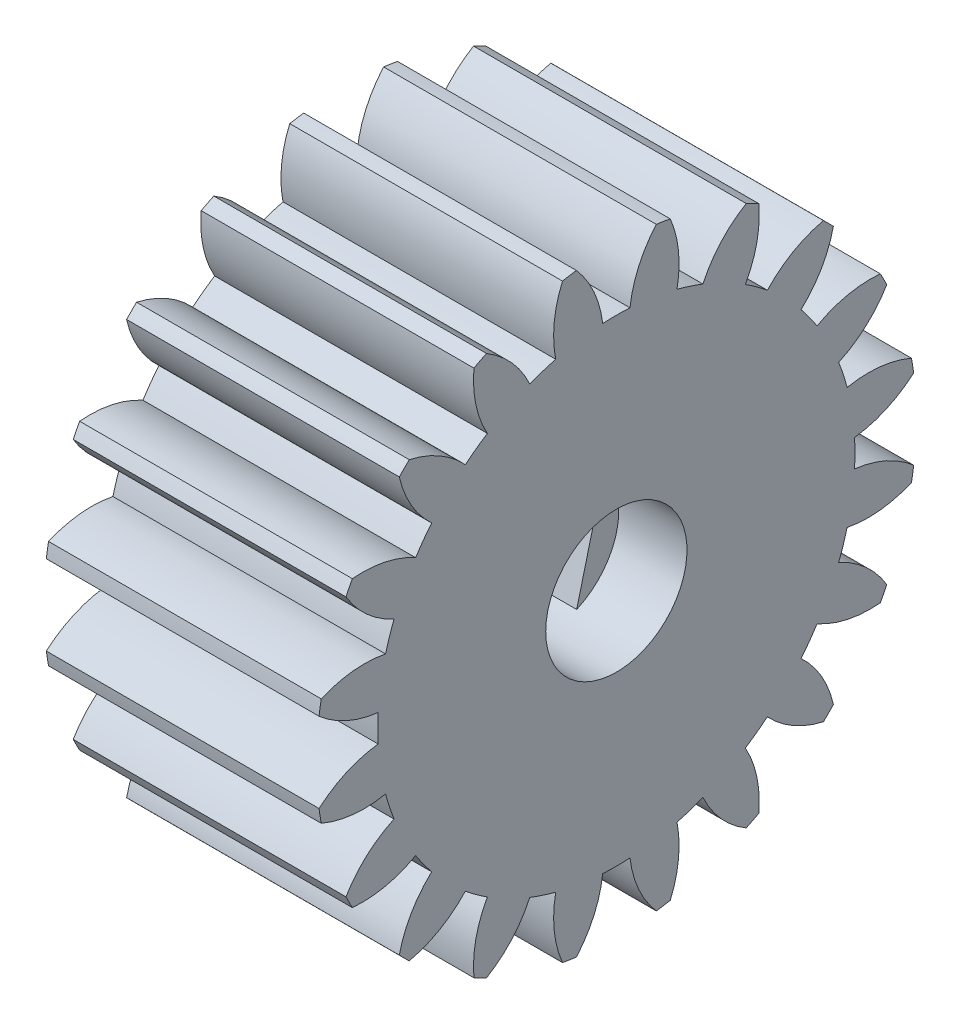
SolidWorks part; units mm, degrees
material "PLA"
ref_plane "Front Plane" through (0, 0, 0) normal (0, 0, 1) x (1, 0, 0)
ref_plane "Top Plane" through (0, 0, 0) normal (0, 1, 0) x (1, 0, 0)
ref_plane "Right Plane" through (0, 0, 0) normal (1, 0, 0) x (0, 0, -1)
ref_plane "Plane1" through (0, 0, 0) normal (0, 0, -1) x (-1, 0, 0)
sketch "Sketch1" plane through (0, 0, 0) normal (0, 0, -1) x (-1, 0, 0)
  line L0 (-10, 11) -> (-10, 0)
  line L1 (-10, 0) -> (0, 0)
  line L2 (0, 0) -> (0, 11)
  line L3 (0, 11) -> (-10, 11)
  line L4 (-10, 0) -> (0, 0) construction
revolve "Revolve1" add sketch "Sketch1" angle 360 about L4
sketch "Sketch2" plane through (0, 0, 0) normal (-1, 0, 0) x (0, 0, 1)
  arc A0 (10.8211, -1.9757) -> (8.4617, -2.2237) centre (9.242, 1.6994) cw
  arc A1 (8.4617, -2.2237) -> (8.1527, -3.1746) centre (0, 0) cw
  arc A2 (8.1527, -3.1746) -> (9.9157, -4.7622) centre (6.478, -6.8072) cw
  arc A3 (9.9157, -4.7622) -> (10.8211, -1.9757) centre (0, 0) ccw
extrude "Cut-Extrude1" cut sketch "Sketch2" against normal through all
sketch "Sketch3" plane through (0, 0, 0) normal (-1, 0, 0) x (0, 0, 1)
  arc A0 (9.681, -5.2229) -> (7.3604, -4.7297) centre (9.3148, -1.2397) cw
  arc A1 (7.3604, -4.7297) -> (6.7727, -5.5386) centre (0, 0) cw
  arc A2 (6.7727, -5.5386) -> (7.9588, -7.5932) centre (4.0574, -8.4758) cw
  arc A3 (7.9588, -7.5932) -> (9.681, -5.2229) centre (0, 0) ccw
extrude "Cut-Extrude2" cut sketch "Sketch3" against normal through all
sketch "Sketch4" plane through (0, 0, 0) normal (-1, 0, 0) x (0, 0, 1)
  arc A0 (5.2229, -9.681) -> (7.5932, -7.9588) centre (0, 0) ccw
  arc A1 (7.5932, -7.9588) -> (5.5386, -6.7727) centre (8.4758, -4.0574) cw
  arc A2 (5.5386, -6.7727) -> (4.7297, -7.3604) centre (0, 0) cw
  arc A3 (4.7297, -7.3604) -> (5.2229, -9.681) centre (1.2397, -9.3148) cw
extrude "Cut-Extrude3" cut sketch "Sketch4" against normal through all
sketch "Sketch5" plane through (0, 0, 0) normal (-1, 0, 0) x (0, 0, 1)
  arc A0 (1.9757, -10.8211) -> (4.7622, -9.9157) centre (0, 0) ccw
  arc A1 (4.7622, -9.9157) -> (3.1746, -8.1527) centre (6.8072, -6.478) cw
  arc A2 (3.1746, -8.1527) -> (2.2237, -8.4617) centre (0, 0) cw
  arc A3 (2.2237, -8.4617) -> (1.9757, -10.8211) centre (-1.6994, -9.242) cw
extrude "Cut-Extrude4" cut sketch "Sketch5" against normal through all
sketch "Sketch6" plane through (0, 0, 0) normal (-1, 0, 0) x (0, 0, 1)
  arc A0 (1.465, -10.902) -> (0.4999, -8.7347) centre (4.4722, -8.2645) cw
  arc A1 (0.4999, -8.7347) -> (-0.4999, -8.7347) centre (0, 0) cw
  arc A2 (-0.4999, -8.7347) -> (-1.465, -10.902) centre (-4.4722, -8.2645) cw
  arc A3 (-1.465, -10.902) -> (1.465, -10.902) centre (0, 0) ccw
extrude "Cut-Extrude5" cut sketch "Sketch6" against normal through all
sketch "Sketch7" plane through (0, 0, 0) normal (-1, 0, 0) x (0, 0, 1)
  arc A0 (-1.9757, -10.8211) -> (-2.2237, -8.4617) centre (1.6994, -9.242) cw
  arc A1 (-2.2237, -8.4617) -> (-3.1746, -8.1527) centre (0, 0) cw
  arc A2 (-3.1746, -8.1527) -> (-4.7622, -9.9157) centre (-6.8072, -6.478) cw
  arc A3 (-4.7622, -9.9157) -> (-1.9757, -10.8211) centre (0, 0) ccw
extrude "Cut-Extrude6" cut sketch "Sketch7" against normal through all
sketch "Sketch8" plane through (0, 0, 0) normal (-1, 0, 0) x (0, 0, 1)
  arc A0 (-5.2229, -9.681) -> (-4.7297, -7.3604) centre (-1.2397, -9.3148) cw
  arc A1 (-4.7297, -7.3604) -> (-5.5386, -6.7727) centre (0, 0) cw
  arc A2 (-5.5386, -6.7727) -> (-7.5932, -7.9588) centre (-8.4758, -4.0574) cw
  arc A3 (-7.5932, -7.9588) -> (-5.2229, -9.681) centre (0, 0) ccw
extrude "Cut-Extrude7" cut sketch "Sketch8" against normal through all
sketch "Sketch9" plane through (0, 0, 0) normal (-1, 0, 0) x (0, 0, 1)
  arc A0 (-7.9588, -7.5932) -> (-6.7727, -5.5386) centre (-4.0574, -8.4758) cw
  arc A1 (-6.7727, -5.5386) -> (-7.3604, -4.7297) centre (0, 0) cw
  arc A2 (-7.3604, -4.7297) -> (-9.681, -5.2229) centre (-9.3148, -1.2397) cw
  arc A3 (-9.681, -5.2229) -> (-7.9588, -7.5932) centre (0, 0) ccw
extrude "Cut-Extrude8" cut sketch "Sketch9" against normal through all
sketch "Sketch10" plane through (0, 0, 0) normal (-1, 0, 0) x (0, 0, 1)
  arc A0 (-9.9157, -4.7622) -> (-8.1527, -3.1746) centre (-6.478, -6.8072) cw
  arc A1 (-8.1527, -3.1746) -> (-8.4617, -2.2237) centre (0, 0) cw
  arc A2 (-8.4617, -2.2237) -> (-10.8211, -1.9757) centre (-9.242, 1.6994) cw
  arc A3 (-10.8211, -1.9757) -> (-9.9157, -4.7622) centre (0, 0) ccw
extrude "Cut-Extrude9" cut sketch "Sketch10" against normal through all
sketch "Sketch11" plane through (0, 0, 0) normal (-1, 0, 0) x (0, 0, 1)
  arc A0 (-10.902, -1.465) -> (-8.7347, -0.4999) centre (-8.2645, -4.4722) cw
  arc A1 (-8.7347, -0.4999) -> (-8.7347, 0.4999) centre (0, 0) cw
  arc A2 (-8.7347, 0.4999) -> (-10.902, 1.465) centre (-8.2645, 4.4722) cw
  arc A3 (-10.902, 1.465) -> (-10.902, -1.465) centre (0, 0) ccw
extrude "Cut-Extrude10" cut sketch "Sketch11" against normal through all
sketch "Sketch12" plane through (0, 0, 0) normal (-1, 0, 0) x (0, 0, 1)
  arc A0 (-10.8211, 1.9757) -> (-8.4617, 2.2237) centre (-9.242, -1.6994) cw
  arc A1 (-8.4617, 2.2237) -> (-8.1527, 3.1746) centre (0, 0) cw
  arc A2 (-8.1527, 3.1746) -> (-9.9157, 4.7622) centre (-6.478, 6.8072) cw
  arc A3 (-9.9157, 4.7622) -> (-10.8211, 1.9757) centre (0, 0) ccw
extrude "Cut-Extrude11" cut sketch "Sketch12" against normal through all
sketch "Sketch13" plane through (0, 0, 0) normal (-1, 0, 0) x (0, 0, 1)
  arc A0 (-9.681, 5.2229) -> (-7.3604, 4.7297) centre (-9.3148, 1.2397) cw
  arc A1 (-7.3604, 4.7297) -> (-6.7727, 5.5386) centre (0, 0) cw
  arc A2 (-6.7727, 5.5386) -> (-7.9588, 7.5932) centre (-4.0574, 8.4758) cw
  arc A3 (-7.9588, 7.5932) -> (-9.681, 5.2229) centre (0, 0) ccw
extrude "Cut-Extrude12" cut sketch "Sketch13" against normal through all
sketch "Sketch14" plane through (0, 0, 0) normal (-1, 0, 0) x (0, 0, 1)
  arc A0 (-7.5932, 7.9588) -> (-5.5386, 6.7727) centre (-8.4758, 4.0574) cw
  arc A1 (-5.5386, 6.7727) -> (-4.7297, 7.3604) centre (0, 0) cw
  arc A2 (-4.7297, 7.3604) -> (-5.2229, 9.681) centre (-1.2397, 9.3148) cw
  arc A3 (-5.2229, 9.681) -> (-7.5932, 7.9588) centre (0, 0) ccw
extrude "Cut-Extrude13" cut sketch "Sketch14" against normal through all
sketch "Sketch15" plane through (0, 0, 0) normal (-1, 0, 0) x (0, 0, 1)
  arc A0 (-4.7622, 9.9157) -> (-3.1746, 8.1527) centre (-6.8072, 6.478) cw
  arc A1 (-3.1746, 8.1527) -> (-2.2237, 8.4617) centre (0, 0) cw
  arc A2 (-2.2237, 8.4617) -> (-1.9757, 10.8211) centre (1.6994, 9.242) cw
  arc A3 (-1.9757, 10.8211) -> (-4.7622, 9.9157) centre (0, 0) ccw
extrude "Cut-Extrude14" cut sketch "Sketch15" against normal through all
sketch "Sketch16" plane through (0, 0, 0) normal (-1, 0, 0) x (0, 0, 1)
  arc A0 (-1.465, 10.902) -> (-0.4999, 8.7347) centre (-4.4722, 8.2645) cw
  arc A1 (-0.4999, 8.7347) -> (0.4999, 8.7347) centre (0, 0) cw
  arc A2 (0.4999, 8.7347) -> (1.465, 10.902) centre (4.4722, 8.2645) cw
  arc A3 (1.465, 10.902) -> (-1.465, 10.902) centre (0, 0) ccw
extrude "Cut-Extrude15" cut sketch "Sketch16" against normal through all
sketch "Sketch17" plane through (0, 0, 0) normal (-1, 0, 0) x (0, 0, 1)
  arc A0 (1.9757, 10.8211) -> (2.2237, 8.4617) centre (-1.6994, 9.242) cw
  arc A1 (2.2237, 8.4617) -> (3.1746, 8.1527) centre (0, 0) cw
  arc A2 (3.1746, 8.1527) -> (4.7622, 9.9157) centre (6.8072, 6.478) cw
  arc A3 (4.7622, 9.9157) -> (1.9757, 10.8211) centre (0, 0) ccw
extrude "Cut-Extrude16" cut sketch "Sketch17" against normal through all
sketch "Sketch18" plane through (0, 0, 0) normal (-1, 0, 0) x (0, 0, 1)
  arc A0 (5.2229, 9.681) -> (4.7297, 7.3604) centre (1.2397, 9.3148) cw
  arc A1 (4.7297, 7.3604) -> (5.5386, 6.7727) centre (0, 0) cw
  arc A2 (5.5386, 6.7727) -> (7.5932, 7.9588) centre (8.4758, 4.0574) cw
  arc A3 (7.5932, 7.9588) -> (5.2229, 9.681) centre (0, 0) ccw
extrude "Cut-Extrude17" cut sketch "Sketch18" against normal through all
sketch "Sketch19" plane through (0, 0, 0) normal (-1, 0, 0) x (0, 0, 1)
  arc A0 (7.9588, 7.5932) -> (6.7727, 5.5386) centre (4.0574, 8.4758) cw
  arc A1 (6.7727, 5.5386) -> (7.3604, 4.7297) centre (0, 0) cw
  arc A2 (7.3604, 4.7297) -> (9.681, 5.2229) centre (9.3148, 1.2397) cw
  arc A3 (9.681, 5.2229) -> (7.9588, 7.5932) centre (0, 0) ccw
extrude "Cut-Extrude18" cut sketch "Sketch19" against normal through all
sketch "Sketch20" plane through (0, 0, 0) normal (-1, 0, 0) x (0, 0, 1)
  arc A0 (9.9157, 4.7622) -> (8.1527, 3.1746) centre (6.478, 6.8072) cw
  arc A1 (8.1527, 3.1746) -> (8.4617, 2.2237) centre (0, 0) cw
  arc A2 (8.4617, 2.2237) -> (10.8211, 1.9757) centre (9.242, -1.6994) cw
  arc A3 (10.8211, 1.9757) -> (9.9157, 4.7622) centre (0, 0) ccw
extrude "Cut-Extrude19" cut sketch "Sketch20" against normal through all
sketch "Sketch21" plane through (0, 0, 0) normal (-1, 0, 0) x (0, 0, 1)
  arc A0 (10.902, 1.465) -> (8.7347, 0.4999) centre (8.2645, 4.4722) cw
  arc A1 (8.7347, 0.4999) -> (8.7347, -0.4999) centre (0, 0) cw
  arc A2 (8.7347, -0.4999) -> (10.902, -1.465) centre (8.2645, -4.4722) cw
  arc A3 (10.902, -1.465) -> (10.902, 1.465) centre (0, 0) ccw
extrude "Cut-Extrude20" cut sketch "Sketch21" against normal through all
hole_wizard "Hole1" positions "Sketch23" profile "Sketch22" legacy
sketch "Sketch23" plane through (0, 0, 0) normal (-1, 0, 0) x (0, 0, 1)
  point P0 (0, 0)
sketch "Sketch22" plane through (0, 0, 0) normal (0, 1, 0) x (0, 0, 1)
  line L0 (0, 0) -> (0, 10)
  line L1 (0, 10) -> (2.59, 10)
  line L2 (2.59, 10) -> (2.59, 0)
  line L3 (2.59, 0) -> (0, 0)
  line L4 (0, 110) -> (0, -10) construction
  dimension "Diameter" = 5.18
  dimension "Depth" = 10
ref_plane "Plane2" through (0, 0, 0) normal (-1, 0, 0) x (0, -1, 0)
sketch "Sketch24" plane through (0, 0, 0) normal (-1, 0, 0) x (0, -1, 0)
  line L0 (-2.3694, 1.0459) -> (1.5771, 2.0545)
  arc A0 (1.5771, 2.0545) -> (-2.3694, 1.0459) centre (0, 0) ccw
extrude "Boss-Extrude1" add sketch "Sketch24" against normal blind 7.5
sketch "Sketch25" plane through (0, 0, 0) normal (-1, 0, 0) x (0, -1, 0)
  line L0 (2.3694, -1.0459) -> (-1.5771, -2.0545)
  arc A0 (-1.5771, -2.0545) -> (2.3694, -1.0459) centre (0, 0) ccw
extrude "Boss-Extrude2" add sketch "Sketch25" against normal blind 7.5
